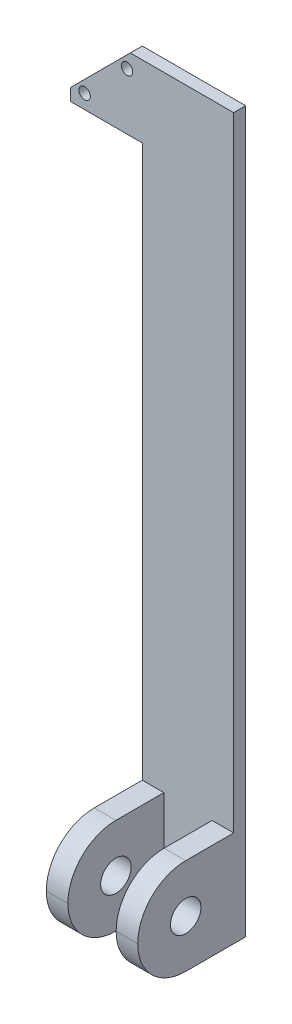
SolidWorks part; units mm, degrees
ref_plane "Front Plane" through (0, 0, 0) normal (0, 0, 1) x (1, 0, 0)
ref_plane "Top Plane" through (0, 0, 0) normal (0, 1, 0) x (1, 0, 0)
ref_plane "Right Plane" through (0, 0, 0) normal (1, 0, 0) x (0, 0, -1)
sketch "Sketch1" plane through (0, 0, 0) normal (0, 0, 1) x (1, 0, 0)
  line L0 (-30, 270) -> (0, 300)
  line L1 (0, 0) -> (38.1, 0)
  line L2 (0, 0) -> (0, 300)
  line L3 (0, 300) -> (38.1, 300)
  line L4 (38.1, 0) -> (38.1, 300)
  line L5 (0, 300) -> (-30, 300)
  line L6 (0, 300) -> (0, 270)
  line L7 (0, 270) -> (-30, 270)
  line L8 (-30, 300) -> (-30, 270)
  line L9 (-30, 275) -> (-5, 300)
  circle A0 centre (-6.364, 293.636) radius 2.3813
  circle A1 centre (-24.0416, 275.9584) radius 2.3813
  dimension "D5" = 4.7625
  dimension "D6" = 4.7625
  dimension "D1" = 300
  dimension "D2" = 38.1
  dimension "D3" = 30
  dimension "D4" = 30
  dimension "D7" = 25
  dimension "D8" = 9
  dimension "D9" = 5
  dimension "D10" = 5
extrude "Boss-Extrude1" add sketch "Sketch1" along normal blind 5 contours A1 L0 A0 L5 L9 L8 | A1 L0 L7 L2 A0 | L1 L4 L3 L2
sketch "Sketch2" plane through (0, 0, 5) normal (0, 0, 1) x (1, 0, 0)
  line L0 (38.1, 0) -> (38.1, 300) construction
  line L1 (0, 0) -> (38.1, 0)
  line L2 (0, 0) -> (0, 40)
  line L3 (0, 40) -> (38.1, 40)
  line L4 (38.1, 0) -> (38.1, 40)
  line L6 (9, 40) -> (29.1, 40)
  line L7 (9, 40) -> (9, 0)
  line L8 (9, 0) -> (29.1, 0)
  line L9 (29.1, 40) -> (29.1, 0)
  dimension "D1" = 40
  dimension "D2" = 9
  dimension "D3" = 9
  dimension "D4" = 20.1
extrude "Boss-Extrude2" add sketch "Sketch2" along normal blind 40 contours L7 L3 M9 M10 | L3 L9 M10 M11
sketch "Sketch3" plane through (38.1, 0, 0) normal (1, 0, 0) x (0, 0, -1)
  line L0 (-5, 40) -> (-45, 0)
  line L1 (-25.01, 0) -> (-5, 0)
  line L2 (-45, 19.99) -> (-45, 20.01)
  line L3 (-25.01, 40) -> (-5, 40)
  line L4 (-5, 0) -> (-5, 40)
  circle A0 centre (-25, 20) radius 6.35
  arc A1 (-25.01, 0) -> (-45, 19.99) centre (-25.01, 19.99) cw
  arc A2 (-45, 20.01) -> (-25.01, 40) centre (-25.01, 20.01) cw
  dimension "D1" = 12.7
  dimension "D2" = 19.99
extrude "Cut-Extrude1" cut sketch "Sketch3" against normal blind 40 contours L0 A0 | L0 A0 | A2 M11 M10 | L0 A1 M11 | A1 L0 M12
